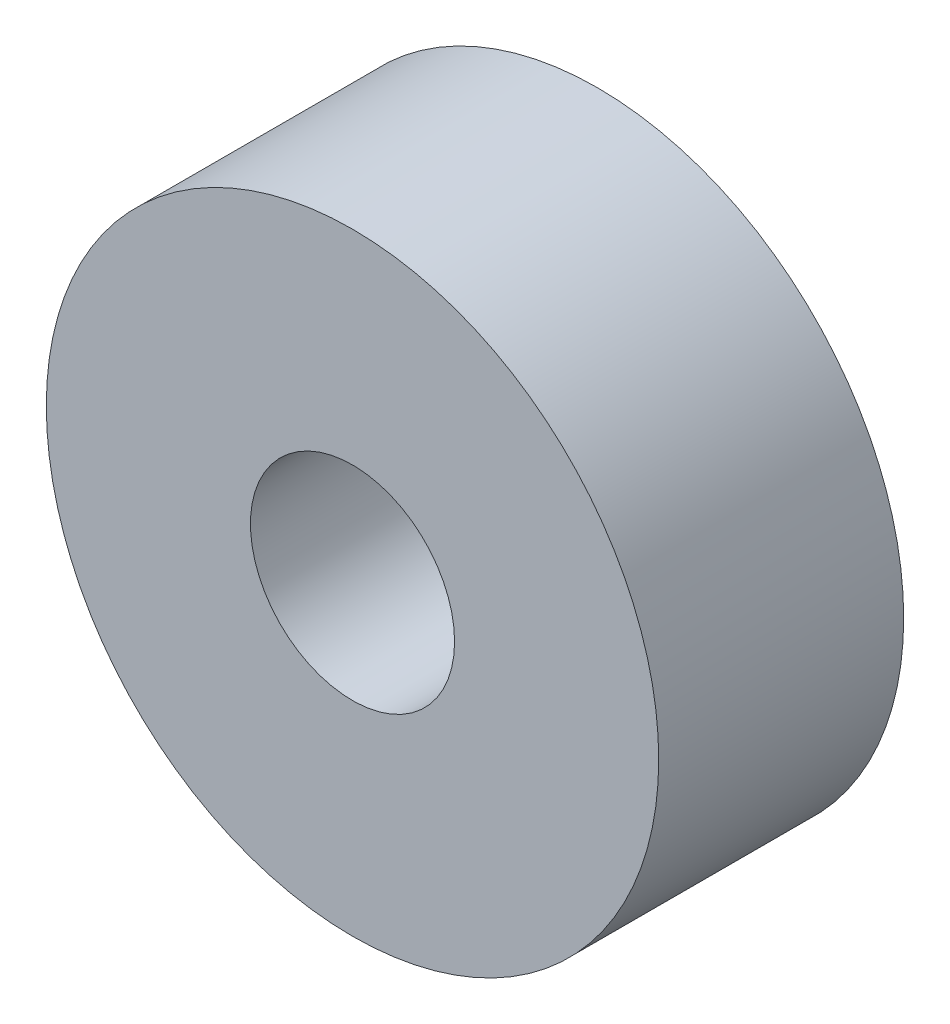
SolidWorks part; units mm, degrees
ref_plane "Front Plane" through (0, 0, 0) normal (0, 0, 1) x (1, 0, 0)
ref_plane "Top Plane" through (0, 0, 0) normal (0, 1, 0) x (1, 0, 0)
ref_plane "Right Plane" through (0, 0, 0) normal (1, 0, 0) x (0, 0, -1)
sketch "Sketch1" plane through (0, 0, 0) normal (0, 0, 1) x (1, 0, 0)
  circle A0 centre (0, 0) radius 2.5
  circle A1 centre (0, 0) radius 7.5
  dimension "D1" = 15
  dimension "D2" = 5
extrude "Boss-Extrude1" add sketch "Sketch1" along normal blind 6
